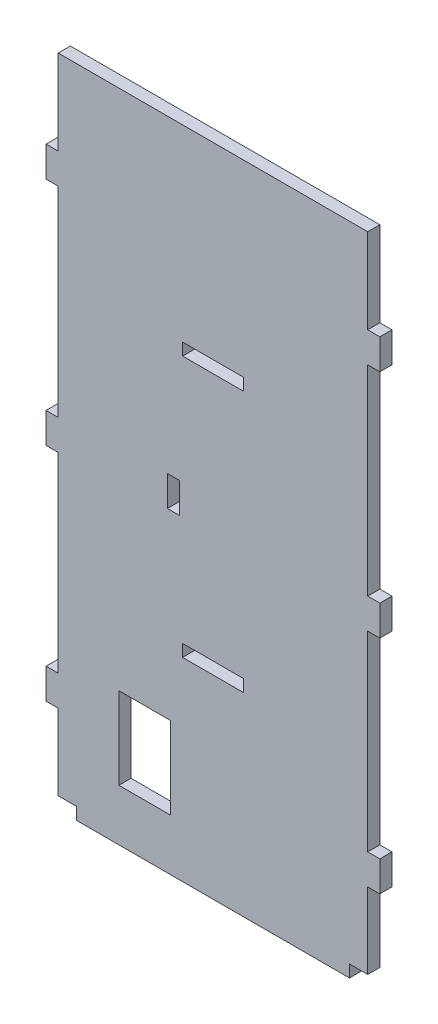
SolidWorks part; units mm, degrees
ref_plane "Front Plane" through (0, 0, 0) normal (0, 0, 1) x (1, 0, 0)
ref_plane "Top Plane" through (0, 0, 0) normal (0, 1, 0) x (1, 0, 0)
ref_plane "Right Plane" through (0, 0, 0) normal (1, 0, 0) x (0, 0, -1)
sketch "Sketch1" plane through (0, 0, 0) normal (0, 0, 1) x (1, 0, 0)
  line L0 (0, 0) -> (3, 0)
  line L5 (3, 0) -> (3, -2)
  line L6 (3, -2) -> (48, -2)
  line L7 (48, -2) -> (48, 0)
  line L8 (48, 0) -> (51, 0)
  line L9 (51, 0) -> (51, 12.5)
  line L10 (51, 12.5) -> (53, 12.5)
  line L11 (53, 12.5) -> (53, 17.5)
  line L12 (53, 17.5) -> (51, 17.5)
  line L13 (51, 17.5) -> (51, 49)
  line L14 (51, 49) -> (53, 49)
  line L15 (53, 49) -> (53, 54)
  line L16 (53, 54) -> (51, 54)
  line L17 (51, 54) -> (51, 87)
  line L18 (51, 87) -> (53, 87)
  line L19 (53, 87) -> (53, 92)
  line L20 (53, 92) -> (51, 92)
  line L21 (51, 92) -> (51, 106)
  line L27 (0, 106) -> (0, 92)
  line L28 (0, 92) -> (-2, 92)
  line L29 (-2, 92) -> (-2, 87)
  line L30 (-2, 87) -> (0, 87)
  line L31 (0, 87) -> (0, 54)
  line L32 (0, 54) -> (-2, 54)
  line L33 (-2, 54) -> (-2, 49)
  line L34 (-2, 49) -> (0, 49)
  line L35 (0, 49) -> (0, 17.5)
  line L36 (0, 17.5) -> (-2, 17.5)
  line L37 (-2, 17.5) -> (-2, 12.5)
  line L38 (-2, 12.5) -> (0, 12.5)
  line L39 (0, 12.5) -> (0, 0)
  line L40 (0, 30) -> (51, 30) construction
  line L41 (0, 32) -> (51, 32) construction
  line L42 (0, 73) -> (51, 73) construction
  line L43 (0, 55) -> (18, 55) construction
  line L44 (20.5, 32) -> (30.5, 32)
  line L45 (20.5, 32) -> (20.5, 30)
  line L46 (20.5, 30) -> (30.5, 30)
  line L47 (30.5, 32) -> (30.5, 30)
  line L48 (20.5, 73) -> (30.5, 73)
  line L49 (20.5, 73) -> (20.5, 75)
  line L50 (20.5, 75) -> (30.5, 75)
  line L51 (30.5, 73) -> (30.5, 75)
  line L52 (18, 55) -> (51, 55) construction
  line L53 (0, 106) -> (51, 106)
  line L54 (18, 55) -> (20, 55)
  line L55 (18, 55) -> (18, 50)
  line L56 (18, 50) -> (20, 50)
  line L57 (20, 55) -> (20, 50)
  line L59 (10, 6.5) -> (18.5, 6.5)
  line L60 (10, 6.5) -> (10, 20)
  line L61 (10, 20) -> (18.5, 20)
  line L62 (18.5, 6.5) -> (18.5, 20)
  point P51 (25.5, 32)
  point P52 (25.5, 73)
  dimension "D1" = 51
  dimension "D2" = 3
  dimension "D3" = 12.5
  dimension "D4" = 5
  dimension "D5" = 2
  dimension "D6" = 31.5
  dimension "D7" = 33
  dimension "D8" = 14
  dimension "D9" = 30
  dimension "D10" = 2
  dimension "D11" = 41
  dimension "D12" = 10
  dimension "D13" = 33
  dimension "D14" = 2
  dimension "D15" = 18
  dimension "D16" = 45
  dimension "D17" = 8.5
  dimension "D18" = 13.5
  dimension "D19" = 10
  dimension "D20" = 10
extrude "Boss-Extrude1" add sketch "Sketch1" along normal blind 2
